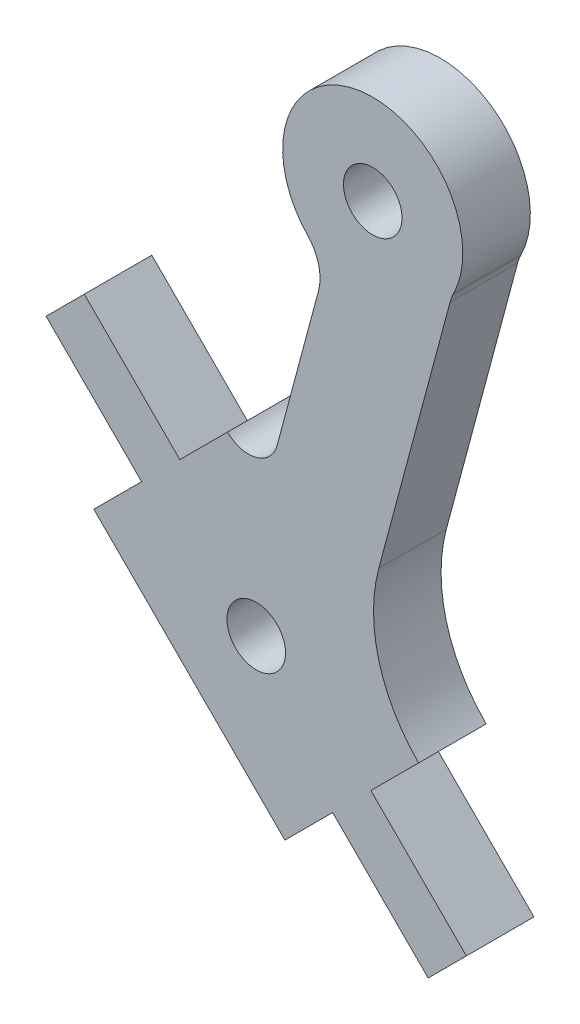
SolidWorks part; units mm, degrees
ref_plane "Front Plane" through (0, 0, 0) normal (0, 0, 1) x (1, 0, 0)
ref_plane "Top Plane" through (0, 0, 0) normal (0, 1, 0) x (1, 0, 0)
ref_plane "Right Plane" through (0, 0, 0) normal (1, 0, 0) x (0, 0, -1)
sketch "Model" plane through (0, 0, 0) normal (0, 0, 1) x (1, 0, 0)
  line L0 (40.054, 38.2637) -> (41.7509, 39.961)
  line L1 (57.0257, 21.2944) -> (58.7227, 22.9916)
  line L2 (44.2969, 34.0214) -> (42.1757, 31.9)
  line L3 (45.9939, 35.7186) -> (48.115, 37.8401)
  line L4 (54.4797, 27.234) -> (56.6009, 29.3554)
  line L5 (52.7828, 25.5367) -> (50.6616, 23.4154)
  line L6 (45.9939, 35.7186) -> (41.7509, 39.961)
  line L7 (44.2969, 34.0214) -> (40.054, 38.2637)
  line L8 (58.7227, 22.9916) -> (54.4797, 27.234)
  line L9 (57.0257, 21.2944) -> (52.7828, 25.5367)
  line L10 (52.1544, 45.2869) -> (50.3177, 38.4305)
  line L11 (57.9994, 47.7837) -> (54.8315, 35.9572)
  line L12 (42.1757, 31.9) -> (50.6616, 23.4154)
  circle A0 centre (49.3883, 30.6277) radius 1.3
  circle A1 centre (54.5633, 49.9466) radius 1.3
  arc A2 (58.142, 48.1596) -> (51.6694, 47.1852) centre (54.5633, 49.9466) ccw
  arc A3 (52.1544, 45.2869) -> (51.6694, 47.1852) centre (50.2224, 45.8043) ccw
  arc A4 (58.142, 48.1596) -> (57.9994, 47.7837) centre (59.9341, 47.2649) ccw
  arc A5 (48.115, 37.8401) -> (50.3177, 38.4305) centre (49.0459, 38.7711) ccw
  arc A6 (54.8315, 35.9572) -> (56.6009, 29.3554) centre (61.4332, 34.1886) ccw
extrude "Boss-Extrude1" add sketch "Model" along normal blind 3
